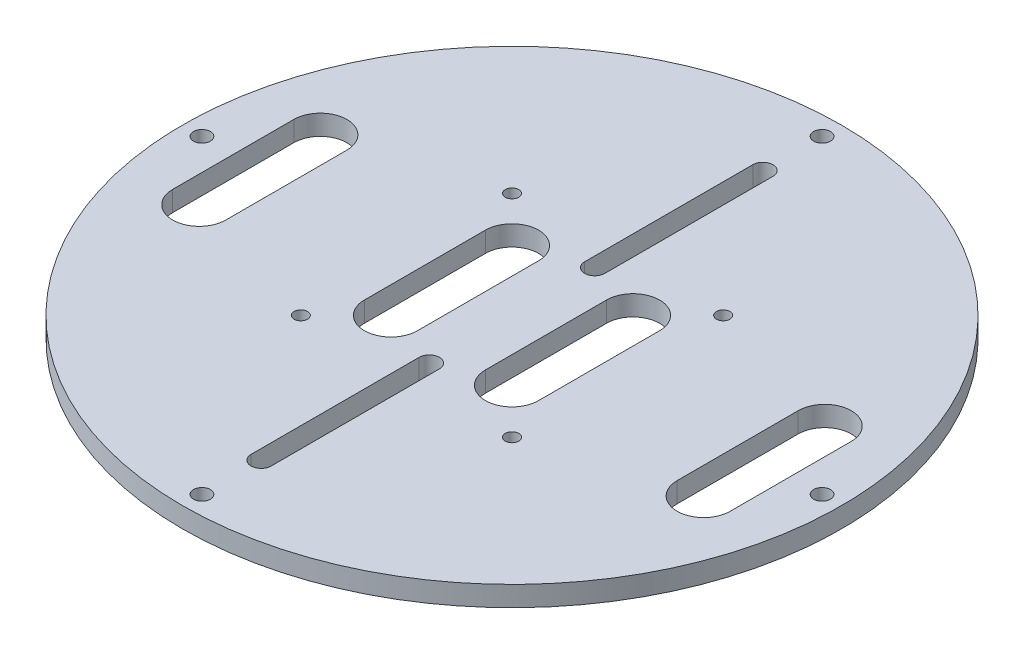
SolidWorks part; units mm, degrees
ref_plane "前视" through (0, 0, 0) normal (0, 0, 1) x (1, 0, 0)
ref_plane "上视" through (0, 0, 0) normal (0, 1, 0) x (1, 0, 0)
ref_plane "右视" through (0, 0, 0) normal (1, 0, 0) x (0, 0, -1)
sketch "草图1" plane through (0, 0, 0) normal (0, 1, 0) x (1, 0, 0)
  circle A0 centre (0, 0) radius 49
  dimension "D1" = 98
extrude "凸台-拉伸1" add sketch "草图1" along normal blind 3
sketch "草图6" plane through (0, 3, 0) normal (0, 1, 0) x (1, 0, 0)
  line L0 (0, 12.3) -> (0, 37.3) construction
  line L1 (-1.5, 12.3) -> (-1.5, 37.3)
  line L2 (1.5, 12.3) -> (1.5, 37.3)
  arc A0 (-1.5, 12.3) -> (1.5, 12.3) centre (0, 12.3) ccw
  arc A1 (1.5, 37.3) -> (-1.5, 37.3) centre (0, 37.3) ccw
  point P3 (0, 24.8)
  dimension "D1" = 25
  dimension "D2" = 12.3
extrude "切除-拉伸1" cut sketch "草图6" against normal through all
pattern_circular "阵列(圆周)2" count 2 over 360 about axis through (0, 0, 0) along (0, 1, 0) of "切除-拉伸1"
sketch "草图7" plane through (0, 3, 0) normal (0, 1, 0) x (1, 0, 0)
  line L0 (-51.2516, 0) -> (52.7908, 0) construction
  line L1 (-17.8863, 15.7) -> (-13.3805, 15.7) construction
  line L2 (-15.7, 17.8338) -> (-15.7, 13.4893) construction
  dimension "D1" = 15.7
  dimension "D2" = 15.7
sketch "草图8" plane through (0, 3, 0) normal (0, 1, 0) x (1, 0, 0)
  line L0 (-17.8863, 15.7) -> (-13.3805, 15.7) construction
  circle A0 centre (-15.7, 15.7) radius 1
  dimension "D1" = 2
sketch "草图9" plane through (0, 3, 0) normal (0, 1, 0) x (1, 0, 0)
  line L0 (-9, 26.2025) -> (-9, -24.6699) construction
  line L1 (-9, -9) -> (-9, 9) construction
  line L2 (-12.95, -9) -> (-12.95, 9)
  line L3 (-5.05, -9) -> (-5.05, 9)
  line L4 (-51.2516, 0) -> (52.7908, 0) construction
  arc A0 (-12.95, -9) -> (-5.05, -9) centre (-9, -9) ccw
  arc A1 (-5.05, 9) -> (-12.95, 9) centre (-9, 9) ccw
  point P4 (-9, 0)
extrude "切除-拉伸3" cut sketch "草图9" against normal through all
pattern_linear "阵列(线性)1" count 2 spacing 28.5 along (-1, 0, 0) of "切除-拉伸3"
pattern_circular "阵列(圆周)5" count 2 over 360 about axis through (0, 0, 0) along (0, 1, 0) of "阵列(线性)1", "切除-拉伸3"
sketch "草图14" plane through (0, 3, 0) normal (0, 1, 0) x (1, 0, 0)
  line L0 (0, 54.6999) -> (0, -58.67) construction
  circle A0 centre (0, 46.1) radius 1.25
  dimension "D1" = 46.1
extrude "切除-拉伸4" cut sketch "草图14" against normal through all
pattern_circular "阵列(圆周)6" count 4 over 360 about axis through (0, 0, 0) along (0, 1, 0) of "切除-拉伸4"
sketch "草图15" plane through (0, 3, 0) normal (0, 1, 0) x (1, 0, 0)
  line L0 (5.1524, -24.8) -> (-5.5286, -24.8) construction
  line L1 (-51.2516, 0) -> (52.7908, 0) construction
  dimension "D1" = 24.8
sketch "草图16" plane through (0, 3, 0) normal (0, 1, 0) x (1, 0, 0)
  line L0 (0, 0) -> (-15.7936, 15.7936) construction
  line L1 (-15.7936, 15.7936) -> (-16.8429, 16.8429) construction
  line L2 (-51.2516, 0) -> (52.7908, 0) construction
  dimension "D1" = 45
extrude "切除-拉伸5" cut sketch "草图8" against normal through all
pattern_circular "阵列(圆周)7" count 4 over 360 about axis through (0, 0, 0) along (0, 1, 0) of "切除-拉伸5"
